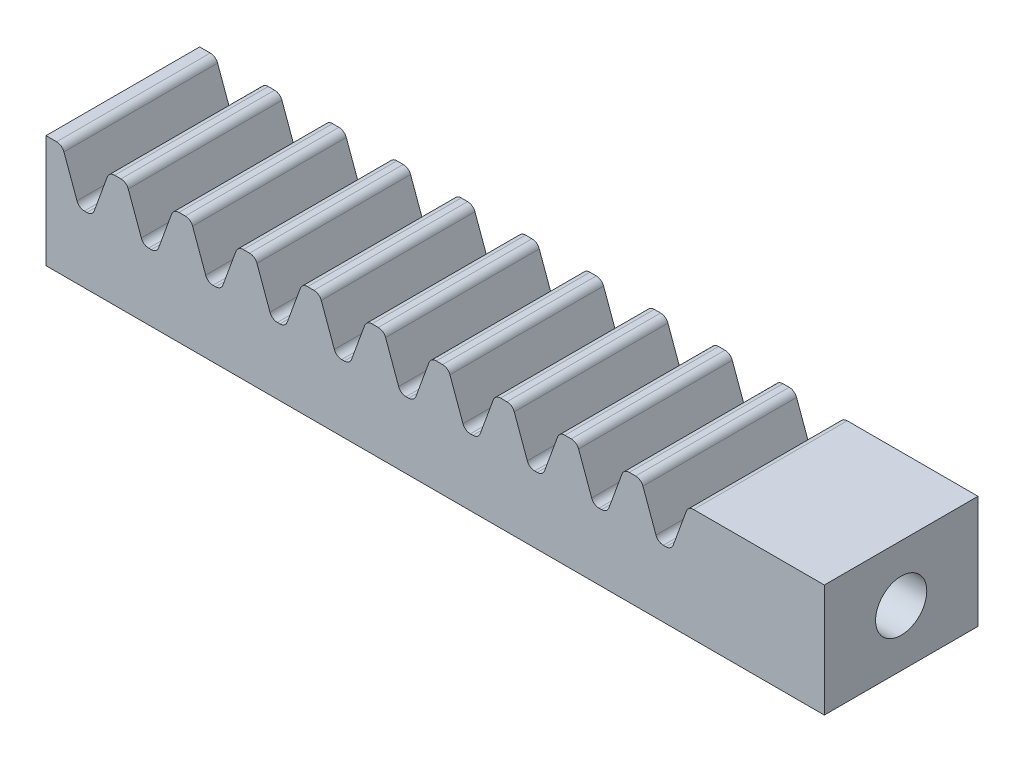
SolidWorks part; units mm, degrees
ref_plane "前视基准面" through (0, 0, 0) normal (0, 0, 1) x (1, 0, 0)
ref_plane "上视基准面" through (0, 0, 0) normal (0, 1, 0) x (1, 0, 0)
ref_plane "右视基准面" through (0, 0, 0) normal (1, 0, 0) x (0, 0, -1)
sketch "草图1" plane through (0, 0, 0) normal (0, 0, 1) x (1, 0, 0)
  line L1 (54, -5.5) -> (-54, -5.5)
  line L2 (54, -5.5) -> (54, 5.5)
  line L3 (54, 5.5) -> (-54, 5.5)
  line L4 (-54, -5.5) -> (-54, 5.5)
  line L5 (54, -5.5) -> (-54, 5.5) construction
  line L6 (54, 5.5) -> (-54, -5.5) construction
  point P0 (0, 0)
  dimension "D1" = 11
extrude "凸台-拉伸1" add sketch "草图1" along normal mid plane 15
sketch "草图2" plane through (0, 0, 7.5) normal (0, 0, 1) x (1, 0, 0)
  line L0 (-52.43, 5.5) -> (-47.8341, 5.5)
  line L1 (54, 5.5) -> (-54, 5.5) construction
  line L2 (-47.8341, 5.5) -> (-49.472, 1)
  line L3 (-49.472, 1) -> (-50.7921, 1)
  line L4 (-50.7921, 1) -> (-52.43, 5.5)
  line L5 (-50.1321, 5.5) -> (-50.1321, 1) construction
  line L6 (-51.7021, 3.5) -> (-48.5621, 3.5) construction
  dimension "D1" = 2
  dimension "D2" = 2.5
  dimension "D3" = 20
  dimension "D4" = 3.14
  dimension "D5" = 1.57
extrude "切除-拉伸1" cut sketch "草图2" against normal through all
fillet "圆角1" radius 0.76 4 edges at (-52.43, 5.5, 0) (-47.8341, 5.5, 0) (-49.472, 1, 0) (-50.7921, 1, 0)
pattern_linear "阵列(线性)1" count 17 spacing 6.28 along (1, 0, 0) of "圆角1", "切除-拉伸1"
ref_plane "基准面1" through (9.42, 0, 0) normal (1, 0, 0) x (0, 0, -1)
sketch "草图3" plane through (9.42, 0, 0) normal (1, 0, 0) x (0, 0, -1)
  line L1 (7.5, -5.5) -> (-7.5, -5.5)
  line L2 (7.5, -5.5) -> (7.5, 5.5)
  line L3 (7.5, 5.5) -> (-7.5, 5.5)
  line L4 (-7.5, -5.5) -> (-7.5, 5.5)
  line L5 (7.5, -5.5) -> (-7.5, 5.5) construction
  line L6 (7.5, 5.5) -> (-7.5, -5.5) construction
  point P0 (0, 0)
extrude "凸台-拉伸2" add sketch "草图3" along normal up to surface (44.58 mm away) up to face at (54, 0, 0)
ref_plane "基准面2" through (21.98, 0, 0) normal (1, 0, 0) x (0, 0, -1)
sketch "草图4" plane through (21.98, 0, 0) normal (1, 0, 0) x (0, 0, -1)
  line L1 (7.5, -5.5) -> (-7.5, -5.5)
  line L2 (7.5, -5.5) -> (7.5, 5.5)
  line L3 (7.5, 5.5) -> (-7.5, 5.5)
  line L4 (-7.5, -5.5) -> (-7.5, 5.5)
  line L5 (7.5, -5.5) -> (-7.5, 5.5) construction
  line L6 (7.5, 5.5) -> (-7.5, -5.5) construction
  point P0 (0, 0)
extrude "切除-拉伸2" cut sketch "草图4" along normal through all
sketch "草图5" plane through (21.98, 0, 0) normal (1, 0, 0) x (0, 0, -1)
  circle A0 centre (0, 0) radius 2.5
extrude "切除-拉伸3" cut sketch "草图5" against normal blind 10
sketch "草图6" plane through (0, 0, 7.5) normal (0, 0, 1) x (1, 0, 0)
  circle A0 centre (17.3069, 0) radius 1
equation "\"m\"=2 '模数"
equation "\"Hax\"=1 '齿顶高系数"
equation "\"Cx\"=0.25 '顶隙系数"
equation "\"Alpha\"=20 '压力角"
equation "\"P\"=Pi*\"m\" '齿距"
equation "\"Ha\"=\"Hax\"*\"m\" '齿顶高"
equation "\"Hf\"=(\"Hax\"+\"Cx\")*\"m\" '齿根高"
equation "\"F\"=0.38*\"m\" '圆角"
